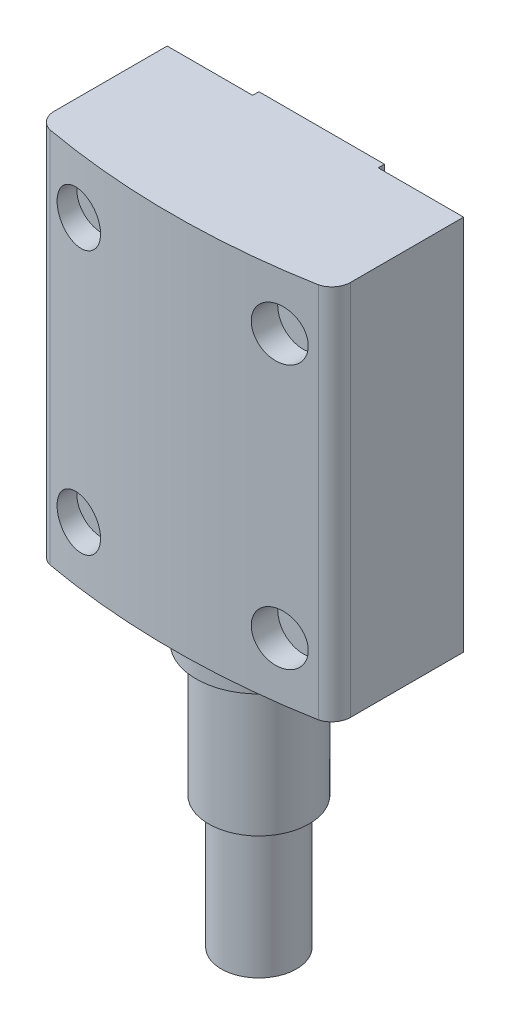
SolidWorks part; units mm, degrees
material "PBT (一般用)"
ref_plane "正面" through (0, 0, 0) normal (0, 0, 1) x (1, 0, 0)
ref_plane "平面" through (0, 0, 0) normal (0, 1, 0) x (1, 0, 0)
ref_plane "右側面" through (0, 0, 0) normal (1, 0, 0) x (0, 0, -1)
sketch "ｽｹｯﾁ1" plane through (0, 0, 0) normal (0, 1, 0) x (1, 0, 0)
  line L0 (-11.8, 4.5) -> (11.8, 4.5)
  line L1 (-11.8, 4.5) -> (-11.8, -4.5)
  line L2 (11.8, 4.5) -> (11.8, -4.5)
  line L3 (-11.8, -4.5) -> (11.8, -4.5)
  line L4 (-11.8, 4.5) -> (11.8, -4.5) construction
  line L5 (11.8, 4.5) -> (-11.8, -4.5) construction
  line L6 (0, -4.5) -> (0, 4.5) construction
  line L7 (5, 5) -> (5, 0.5)
  line L8 (-5, 4.5) -> (-5, 0.5)
  line L10 (-5, 4.5) -> (5, 4.5)
  line L11 (-5, 4.5) -> (-5, 5)
  line L12 (-5, 5) -> (5, 5)
  line L13 (5, 4.5) -> (5, 5)
  arc A0 (11.8, -4.5) -> (10.6882, -5.9489) centre (10.3, -4.5) cw
  arc A1 (-11.8, -4.5) -> (-10.6882, -5.9489) centre (-10.3, -4.5) ccw
  arc A2 (-10.6882, -5.9489) -> (10.6882, -5.9489) centre (0, 53.1093) ccw
  arc A3 (-5, 0.5) -> (5, 0.5) centre (0, 0.5) ccw
  point P1 (0, 0)
extrude "ﾎﾞｽ - 押し出し3" add sketch "ｽｹｯﾁ1" along normal blind 30 contours A3 L8 L0 L1 L3 | A3 L7 L0 L8 | A3 L3 L2 L0 L7 | A1 A2 A0 L3 | L12 L11 L0 L7
sketch "ｽｹｯﾁ4" plane through (0, 0, 0) normal (0, -1, 0) x (1, 0, 0)
  line L0 (0, -5) -> (0, 6.9083) construction
  line L1 (-5, -5) -> (5, -5) construction
  arc A0 (10.6882, 5.9489) -> (-10.6882, 5.9489) centre (0, -53.1093) ccw construction
  circle A1 centre (0, 0) radius 5
extrude "ﾎﾞｽ - 押し出し4" add sketch "ｽｹｯﾁ4" along normal blind 3
sketch "ｽｹｯﾁ5" plane through (0, -3, 0) normal (0, -1, 0) x (1, 0, 0)
  circle A0 centre (0, 0) radius 4
extrude "ﾎﾞｽ - 押し出し5" add sketch "ｽｹｯﾁ5" along normal blind 10.5
sketch "ｽｹｯﾁ6" plane through (0, -13.5, 0) normal (0, -1, 0) x (1, 0, 0)
  circle A0 centre (0, 0) radius 3
extrude "ﾎﾞｽ - 押し出し6" add sketch "ｽｹｯﾁ6" along normal blind 10.5
sketch "ｽｹｯﾁ9" plane through (0, 0, 4.5) normal (0, 0, -1) x (-1, 0, 0)
  circle A0 centre (-8, 4.5) radius 2
  circle A1 centre (8, 4.5) radius 2
  circle A2 centre (8, 25.5) radius 2
  circle A3 centre (-8, 25.5) radius 2
extrude "ｶｯﾄ - 押し出し2" cut sketch "ｽｹｯﾁ9" against normal up to next
